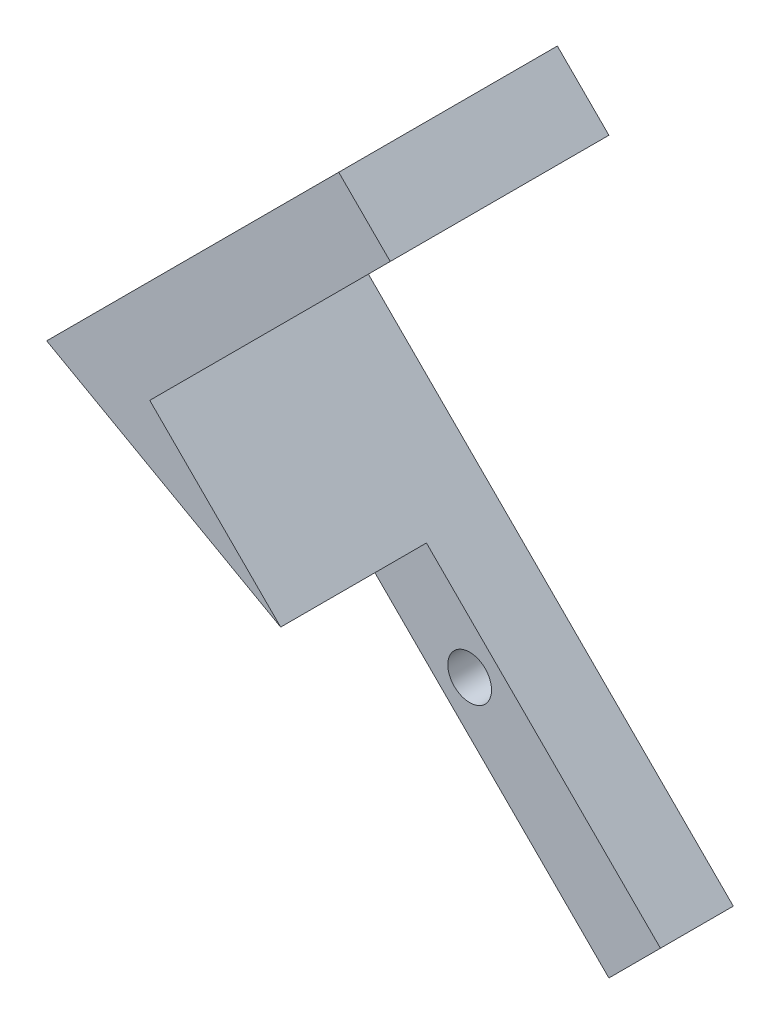
SolidWorks part; units mm, degrees
ref_plane "前视基准面" through (0, 0, 0) normal (0, 0, 1) x (1, 0, 0)
ref_plane "上视基准面" through (0, 0, 0) normal (0, 1, 0) x (1, 0, 0)
ref_plane "右视基准面" through (0, 0, 0) normal (1, 0, 0) x (0, 0, -1)
sketch "草图1" plane through (0, 0, 0) normal (0, 0, 1) x (1, 0, 0)
  line L0 (0, 0) -> (0, 33) construction
  line L1 (0, 33) -> (-16.5, 16.5)
  line L2 (-16.5, 16.5) -> (0, 0)
  line L3 (0, 0) -> (6.0519, -6.0519)
  line L5 (-3.5355, 36.5355) -> (-23.5711, 16.5)
  line L6 (-23.5711, 16.5) -> (5, -12.0711)
  line L7 (-3.5355, -3.5355) -> (2.5163, -9.5874)
  line L8 (5, -12.0711) -> (5, 45.0711) construction
  line L9 (0, 33) -> (-3.5355, 36.5355)
  line L10 (6.0519, -6.0519) -> (8.5355, -8.5355)
  line L11 (5, -12.0711) -> (8.5355, -8.5355)
  line L13 (5, 45.0711) -> (-23.5711, 16.5) construction
  dimension "D1" = 5
extrude "凸台-拉伸1" add sketch "草图1" along normal blind 10 contours L6 L11 L10 L3 L2 L1 L9 L5
sketch "草图2" plane through (0, 0, 10) normal (0, 0, 1) x (1, 0, 0)
  line L0 (-8.25, 24.75) -> (0.2353, 16.2647) construction
  line L1 (0, 33) -> (-16.5, 16.5) construction
  line L2 (0.2353, 4.2647) -> (-7.2365, 4.2647) construction
  line L3 (-2.7828, 2.7828) -> (-6.3183, -0.7527) construction
  line L4 (-16.5, 16.5) -> (8.5355, -8.5355) construction
  line L5 (-23.5711, 16.5) -> (5, -12.0711) construction
  circle A1 centre (-4.5506, 1.015) radius 1.5
extrude "切除-拉伸1" cut sketch "草图2" against normal blind 10
sketch "草图3" plane through (0, 0, 10) normal (0, 0, 1) x (1, 0, 0)
  line L0 (-3.9822, 3.9822) -> (-9.3372, -1.3727)
  line L1 (-16.5, 16.5) -> (8.5355, -8.5355) construction
  line L2 (-9.3372, -1.3727) -> (6.1442, -17.3238)
  line L3 (6.1442, -17.3238) -> (15.0365, -7.3201)
  line L4 (15.0365, -7.3201) -> (-1.5965, 6.368)
  line L5 (-1.5965, 6.368) -> (-4.279, 3.6854)
  circle M1 centre (-4.5506, 1.015) radius 1.5
  line M2 (-23.5711, 16.5) -> (5, -12.0711)
  line M3 (5, -12.0711) -> (8.5355, -8.5355)
  line M4 (8.5355, -8.5355) -> (-16.5, 16.5)
extrude "切除-拉伸4" cut sketch "草图3" against normal blind 5 contours L4 L5 L0 L2 L3 M4 M3 M2 | L0 M4 M2 M3 M1
sketch "草图4" plane through (-3.9822, 3.9822, 0) normal (0.7071, -0.7071, 0) x (0, 0, -1)
  line L0 (-10, 0) -> (0, 0) construction
  line L1 (-5, 0) -> (-10, 0)
  line L2 (-5, 0) -> (-5, -5)
  line L3 (-5, -5) -> (-10, -5)
  line L4 (-10, 0) -> (-10, -5)
extrude "切除-拉伸5" cut sketch "草图4" against normal blind 5
sketch "草图5" plane through (0, 0, 10) normal (0, 0, 1) x (1, 0, 0)
  line L0 (-7.5178, 7.5178) -> (-23.5711, 16.5)
  line L1 (-23.5711, 16.5) -> (-3.5355, 36.5355)
  line L2 (-3.5355, 36.5355) -> (0, 33)
  line L3 (0, 33) -> (-16.5, 16.5)
  line L4 (-16.5, 16.5) -> (-7.5178, 7.5178)
extrude "凸台-拉伸2" add sketch "草图5" along normal blind 5
sketch "草图6" plane through (0, 0, 5) normal (0, 0, 1) x (1, 0, 0)
  line L0 (-3.186, 3.186) -> (-15.2068, 8.1358)
  line L1 (-7.5178, 7.5178) -> (8.5355, -8.5355) construction
  line L2 (-23.5711, 16.5) -> (-11.0533, 3.9822) construction
  line L3 (-15.2068, 8.1358) -> (-23.5711, 16.5)
  line L4 (-23.5711, 16.5) -> (-12.3179, 12.3179)
  line L5 (-7.5178, 7.5178) -> (-16.5, 16.5) construction
  line L6 (-12.3179, 12.3179) -> (-3.186, 3.186)
